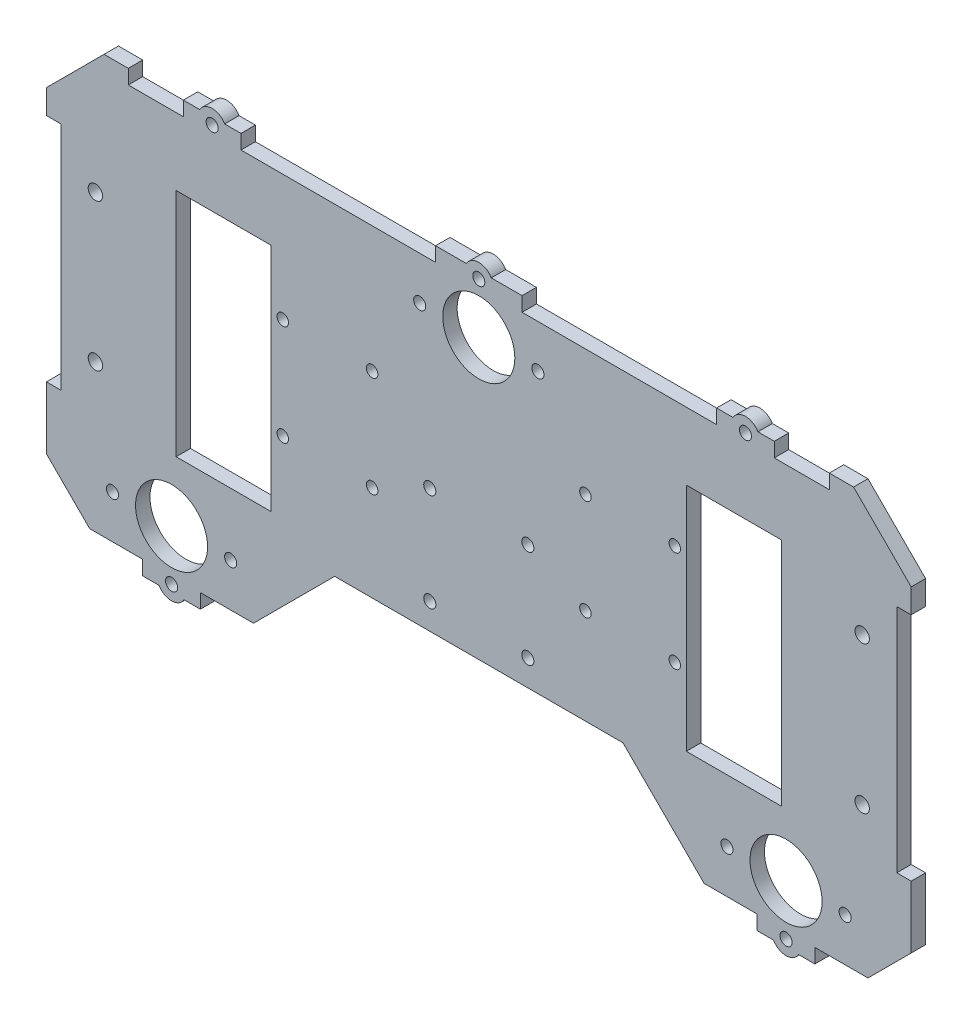
SolidWorks part; units mm, degrees
ref_plane "Front Plane" through (0, 0, 0) normal (0, 0, 1) x (1, 0, 0)
ref_plane "Top Plane" through (0, 0, 0) normal (0, 1, 0) x (1, 0, 0)
ref_plane "Right Plane" through (0, 0, 0) normal (1, 0, 0) x (0, 0, -1)
sketch "Sketch1" plane through (0, 0, 0) normal (0, 0, 1) x (1, 0, 0)
  line L0 (72.8354, 47.1578) -> (72.8354, -32.8422)
  line L1 (105.8354, 47.1578) -> (72.8354, 47.1578)
  line L2 (105.8354, -32.8422) -> (105.8354, 47.1578)
  line L3 (72.8354, -32.8422) -> (105.8354, -32.8422)
  line L4 (84.0016, -74.4431) -> (130.8354, -74.4431)
  line L5 (130.8354, -74.4431) -> (150.8354, -54.4431)
  line L6 (150.8354, -54.4431) -> (150.8354, 55.5569)
  line L7 (150.8354, 55.5569) -> (130.8354, 75.5569)
  line L8 (130.8354, 75.5569) -> (-129.1646, 75.5569)
  line L9 (-129.1646, 75.5569) -> (-149.1646, 55.5569)
  line L10 (-149.1646, 55.5569) -> (-149.1646, -54.4431)
  line L11 (-149.1646, -54.4431) -> (-129.1646, -74.4431)
  line L12 (-129.1646, -74.4431) -> (-82.3309, -74.4431)
  line L13 (-82.3309, -74.4431) -> (-49.1646, -41.2768)
  line L14 (-49.1646, -41.2768) -> (50.8354, -41.2768)
  line L15 (50.8354, -41.2768) -> (84.0016, -74.4431)
  line L16 (-71.1646, -32.8422) -> (-71.1646, 47.1578)
  line L17 (-104.1646, -32.8422) -> (-71.1646, -32.8422)
  line L18 (-104.1646, 47.1578) -> (-104.1646, -32.8422)
  line L19 (-71.1646, 47.1578) -> (-104.1646, 47.1578)
  circle A0 centre (107.4185, -54.4431) radius 12.5
  circle A1 centre (-105.7478, -54.4431) radius 12.5
  circle A2 centre (0.8354, 55.5569) radius 12.5
  dimension "D1" = 45
  dimension "D2" = 45
  dimension "D3" = 28.2843
  dimension "D4" = 110
  dimension "D5" = 28.2843
  dimension "D6" = 46.8338
  dimension "D7" = 46.9042
  dimension "D8" = 100
  dimension "D9" = 46.9042
  dimension "D10" = 46.8338
  dimension "D11" = 28.2843
  dimension "D12" = 110
  dimension "D13" = 28.2843
extrude "Boss-Extrude1" add sketch "Sketch1" along normal blind 5
sketch "Sketch2" plane through (0, 0, 5) normal (0, 0, 1) x (1, 0, 0)
  circle A1 centre (17.3354, -3.2768) radius 1.6
  circle A2 centre (17.3354, -3.2768) radius 1.6
  circle A3 centre (17.3354, -37.2768) radius 1.6
  circle A4 centre (17.3354, -37.2768) radius 1.6
  circle A5 centre (-16.6646, -37.2768) radius 1.6
  circle A6 centre (-16.6646, -37.2768) radius 1.6
  circle A7 centre (-16.6646, -3.2768) radius 1.6
  circle A8 centre (-16.6646, -3.2768) radius 1.6
  dimension "D1" = 0
  dimension "D2" = 0
  dimension "D3" = 0
  dimension "D4" = 0
extrude "Cut-Extrude1" cut sketch "Sketch2" against normal through all
sketch "Sketch4" plane through (0, 0, 5) normal (0, 0, 1) x (1, 0, 0)
  line L0 (150.8354, -54.4431) -> (150.8354, 55.5569) construction
  line L1 (150.8354, 47.1578) -> (145.8354, 47.1578)
  line L2 (150.8354, 47.1578) -> (150.8354, -32.8422)
  line L3 (150.8354, -32.8422) -> (145.8354, -32.8422)
  line L4 (145.8354, 47.1578) -> (145.8354, -32.8422)
  line L5 (105.8354, 47.1578) -> (72.8354, 47.1578) construction
  line L6 (72.8354, -32.8422) -> (105.8354, -32.8422) construction
  line L7 (0.8354, 75.5569) -> (0.8354, 63.8174) construction
  line L8 (130.8354, 75.5569) -> (-129.1646, 75.5569) construction
  line L9 (-144.1646, 47.1578) -> (-144.1646, -32.8422)
  line L10 (-149.1646, -32.8422) -> (-144.1646, -32.8422)
  line L11 (-149.1646, 47.1578) -> (-149.1646, -32.8422)
  line L12 (-149.1646, 47.1578) -> (-144.1646, 47.1578)
  dimension "D1" = 5
extrude "Cut-Extrude3" cut sketch "Sketch4" against normal through all
sketch "Sketch5" plane through (0, 0, 5) normal (0, 0, 1) x (1, 0, 0)
  line L0 (0.8354, 75.5569) -> (0.8354, 46.4183) construction
  line L1 (130.8354, 75.5569) -> (-129.1646, 75.5569) construction
  circle A0 centre (-67.1646, -8.1175) radius 2 construction
  circle A1 centre (-36.1646, -8.1175) radius 2 construction
  circle A2 centre (-36.1646, 26.8825) radius 2 construction
  circle A3 centre (-67.1646, 26.8825) radius 2 construction
  circle A4 centre (-67.1646, -8.1175) radius 2
  circle A5 centre (-36.1646, -8.1175) radius 2
  circle A6 centre (-36.1646, 26.8825) radius 2
  circle A7 centre (-67.1646, 26.8825) radius 2
  circle A8 centre (68.8354, 26.8825) radius 2
  circle A9 centre (37.8354, 26.8825) radius 2
  circle A10 centre (37.8354, -8.1175) radius 2
  circle A11 centre (68.8354, -8.1175) radius 2
extrude "Cut-Extrude4" cut sketch "Sketch5" against normal through all
sketch "Sketch6" plane through (0, 0, 5) normal (0, 0, 1) x (1, 0, 0)
  line L0 (0.8354, 75.5569) -> (0.8354, 62.2242) construction
  line L1 (130.8354, 75.5569) -> (-129.1646, 75.5569) construction
  circle A0 centre (133.8354, -18.3422) radius 2.5 construction
  circle A1 centre (133.8354, 32.6578) radius 2.5 construction
  circle A2 centre (133.8354, -18.3422) radius 2.5
  circle A3 centre (133.8354, 32.6578) radius 2.5
  circle A4 centre (-132.1646, 32.6578) radius 2.5
  circle A5 centre (-132.1646, -18.3422) radius 2.5
extrude "Cut-Extrude5" cut sketch "Sketch6" against normal through all
sketch "Sketch7" plane through (0, 0, 5) normal (0, 0, 1) x (1, 0, 0)
  line L0 (-105.7478, -74.4431) -> (-105.7478, -66.9431) construction
  line L1 (-129.1646, -74.4431) -> (-82.3309, -74.4431) construction
  line L2 (-115.7478, -69.4431) -> (-134.1646, -69.4431)
  line L8 (-115.7478, -74.4431) -> (-115.7478, -69.4431)
  line L10 (-95.7478, -74.4431) -> (-95.7478, -69.4431)
  line L11 (0.8354, -41.2768) -> (0.8354, -58.5234) construction
  line L12 (-49.1646, -41.2768) -> (50.8354, -41.2768) construction
  line L13 (-149.1646, -54.4431) -> (-129.1646, -74.4431) construction
  line L14 (-95.7478, -69.4431) -> (-77.3309, -69.4431)
  line L15 (-82.3309, -74.4431) -> (-49.1646, -41.2768) construction
  line L16 (-134.1646, -69.4431) -> (-129.1646, -74.4431)
  line L17 (-129.1646, -74.4431) -> (-115.7478, -74.4431)
  line L18 (-82.3309, -74.4431) -> (-77.3309, -69.4431)
  line L19 (-95.7478, -74.4431) -> (-82.3309, -74.4431)
  line L20 (107.4185, -74.4431) -> (107.4185, -66.9431) construction
  line L21 (97.4185, -74.4431) -> (84.0016, -74.4431)
  line L22 (84.0016, -74.4431) -> (79.0016, -69.4431)
  line L23 (130.8354, -74.4431) -> (117.4185, -74.4431)
  line L24 (135.8354, -69.4431) -> (130.8354, -74.4431)
  line L25 (97.4185, -69.4431) -> (79.0016, -69.4431)
  line L26 (97.4185, -74.4431) -> (97.4185, -69.4431)
  line L27 (117.4185, -74.4431) -> (117.4185, -69.4431)
  line L28 (117.4185, -69.4431) -> (135.8354, -69.4431)
  circle A0 centre (-105.7478, -54.4431) radius 12.5 construction
  dimension "D1" = 5
  dimension "D2" = 5
  dimension "D3" = 20
  dimension "D4" = 10
extrude "Cut-Extrude7" cut sketch "Sketch7" against normal through all
sketch "Sketch10" plane through (0, 0, 5) normal (0, 0, 1) x (1, 0, 0)
  line L0 (0.8354, 68.0569) -> (0.8354, 75.5569) construction
  line L1 (130.8354, 75.5569) -> (-129.1646, 75.5569) construction
  line L2 (-62.5646, 75.5569) -> (-81.6646, 75.5569) construction
  line L4 (-14.1646, 75.5569) -> (-14.1646, 70.5569)
  line L6 (15.8354, 75.5569) -> (15.8354, 70.5569)
  line L7 (15.8354, 75.5569) -> (64.2354, 75.5569)
  line L8 (15.8354, 75.5569) -> (15.8354, 70.5569)
  line L9 (15.8354, 70.5569) -> (64.2354, 70.5569)
  line L11 (-14.1646, 75.5569) -> (-62.5646, 75.5569)
  line L12 (-14.1646, 75.5569) -> (-14.1646, 70.5569)
  line L13 (-14.1646, 70.5569) -> (-62.5646, 70.5569)
  line L14 (-62.5646, 75.5569) -> (-62.5646, 70.5569)
  line L15 (-91.6646, 75.5569) -> (-91.6646, 70.5569) construction
  line L16 (-101.6646, 75.5569) -> (-120.7646, 75.5569) construction
  line L18 (-101.6646, 75.5569) -> (-101.6646, 70.5569)
  line L20 (-81.6646, 75.5569) -> (-81.6646, 70.5569)
  line L21 (-81.6646, 75.5569) -> (-62.5646, 75.5569)
  line L22 (-81.6646, 75.5569) -> (-81.6646, 70.5569)
  line L23 (-81.6646, 70.5569) -> (-62.5646, 70.5569)
  line L24 (-62.5646, 75.5569) -> (-62.5646, 70.5569)
  line L25 (-101.6646, 75.5569) -> (-120.7646, 75.5569)
  line L26 (-101.6646, 75.5569) -> (-101.6646, 70.5569)
  line L27 (-101.6646, 70.5569) -> (-120.7646, 70.5569)
  line L29 (-120.7646, 75.5569) -> (-120.7646, 70.5569)
  line L30 (15.8354, 75.5569) -> (15.8354, 70.5569)
  line L31 (15.8354, 70.5569) -> (64.2354, 70.5569)
  line L32 (15.8354, 75.5569) -> (64.2354, 75.5569)
  line L33 (83.3354, 75.5569) -> (64.2354, 75.5569)
  line L34 (83.3354, 70.5569) -> (64.2354, 70.5569)
  line L35 (83.3354, 75.5569) -> (83.3354, 70.5569)
  line L36 (103.3354, 75.5569) -> (103.3354, 70.5569)
  line L37 (103.3354, 75.5569) -> (122.4354, 75.5569)
  line L38 (122.4354, 75.5569) -> (122.4354, 70.5569)
  line L39 (103.3354, 70.5569) -> (122.4354, 70.5569)
  line L40 (-149.1646, 55.5569) -> (-149.1646, 47.1578) construction
  line L41 (-149.1646, 55.5569) -> (-149.1646, 47.1578)
  circle A0 centre (0.8354, 55.5569) radius 12.5 construction
  dimension "D1" = 5
  dimension "D2" = 19.1
  dimension "D3" = 15
  dimension "D4" = 19.1
  dimension "D5" = 48.4
  dimension "D10" = 8.4
  dimension "D11" = 5
extrude "Cut-Extrude9" cut sketch "Sketch10" against normal through all contours L25 L29 L27 L18 | L20 L23 L14 L21 | L11 L14 L13 L4 | L35 L33 L7 L6 L9 L34 | L36 L39 L38 L37
sketch "Sketch11" plane through (0, 0, 5) normal (0, 0, 1) x (1, 0, 0)
  line L0 (-14.1646, 75.5569) -> (15.8354, 70.5569) construction
  line L1 (-101.6646, 75.5569) -> (-81.6646, 70.5569) construction
  line L2 (83.3354, 75.5569) -> (103.3354, 70.5569) construction
  line L3 (-115.7478, -74.4431) -> (-95.7478, -69.4431) construction
  line L4 (97.4185, -74.4431) -> (117.4185, -69.4431) construction
  line L5 (97.4185, -74.4431) -> (117.4185, -74.4431) construction
  line L6 (-115.7478, -74.4431) -> (-95.7478, -74.4431) construction
  line L7 (103.3354, 75.5569) -> (83.3354, 75.5569) construction
  line L8 (15.8354, 75.5569) -> (-14.1646, 75.5569) construction
  line L9 (-81.6646, 75.5569) -> (-101.6646, 75.5569) construction
  line L10 (103.0884, -74.4431) -> (111.7486, -74.4431)
  line L11 (-110.0779, -74.4431) -> (-101.4176, -74.4431)
  line L12 (97.6655, 75.5569) -> (89.0052, 75.5569)
  line L13 (5.1655, 75.5569) -> (-3.4948, 75.5569)
  line L14 (-87.3345, 75.5569) -> (-95.9948, 75.5569)
  arc A0 (-87.3345, 75.5569) -> (-95.9948, 75.5569) centre (-91.6646, 73.0569) ccw
  arc A1 (5.1655, 75.5569) -> (-3.4948, 75.5569) centre (0.8354, 73.0569) ccw
  arc A2 (97.6655, 75.5569) -> (89.0052, 75.5569) centre (93.3354, 73.0569) ccw
  arc A3 (-110.0779, -74.4431) -> (-101.4176, -74.4431) centre (-105.7478, -71.9431) ccw
  arc A4 (103.0884, -74.4431) -> (111.7486, -74.4431) centre (107.4185, -71.9431) ccw
  dimension "D1" = 10
  dimension "D2" = 10
  dimension "D3" = 10
  dimension "D4" = 10
  dimension "D5" = 10
extrude "Boss-Extrude3" add sketch "Sketch11" against normal blind 5
sketch "Sketch12" plane through (0, 0, 5) normal (0, 0, 1) x (1, 0, 0)
  line L0 (-14.1646, 75.5569) -> (15.8354, 70.5569) construction
  line L1 (-101.6646, 75.5569) -> (-81.6646, 70.5569) construction
  line L2 (83.3354, 75.5569) -> (103.3354, 70.5569) construction
  line L3 (-115.7478, -69.4431) -> (-95.7478, -74.4431) construction
  line L4 (97.4185, -74.4431) -> (117.4185, -69.4431) construction
  circle A0 centre (107.4185, -71.9431) radius 2.1
  circle A1 centre (-105.7478, -71.9431) radius 2.1
  circle A2 centre (93.3354, 73.0569) radius 2.1
  circle A3 centre (0.8354, 73.0569) radius 2.1
  circle A4 centre (-91.6646, 73.0569) radius 2.1
  dimension "D1" = 4.2
  dimension "D2" = 4.2
  dimension "D3" = 4.2
  dimension "D4" = 4.2
  dimension "D5" = 4.2
extrude "Cut-Extrude10" cut sketch "Sketch12" against normal blind 5
sketch "Sketch13" plane through (0, 0, 5) normal (0, 0, 1) x (1, 0, 0)
  line L0 (-24.269, 55.5569) -> (23.8406, 55.5569) construction
  line L1 (0.8354, -41.2768) -> (0.8354, -57.9375) construction
  line L2 (-49.1646, -41.2768) -> (50.8354, -41.2768) construction
  line L3 (-130.5718, -54.4431) -> (-80.3209, -54.4431) construction
  line L4 (132.2425, -54.4431) -> (81.9916, -54.4431) construction
  circle A0 centre (-19.6646, 55.5569) radius 2.1
  circle A1 centre (21.3354, 55.5569) radius 2.1
  circle A2 centre (-126.2478, -54.4431) radius 2.1
  circle A3 centre (-85.2478, -54.4431) radius 2.1
  circle A5 centre (-105.7478, -54.4431) radius 12.5 construction
  circle A6 centre (0.8354, 55.5569) radius 12.5 construction
  circle A7 centre (86.9185, -54.4431) radius 2.1
  circle A8 centre (127.9185, -54.4431) radius 2.1
  dimension "D1" = 4.2
  dimension "D2" = 20.5
  dimension "D3" = 4.2
  dimension "D4" = 20.5
  dimension "D5" = 4.2
  dimension "D6" = 4.2
  dimension "D7" = 20.5
  dimension "D8" = 20.5
extrude "Cut-Extrude11" cut sketch "Sketch13" against normal blind 5
sketch "Sketch15" plane through (0, 0, 0) normal (0, 0, -1) x (-1, 0, 0)
  circle A1 centre (16.6646, -37.2768) radius 1.6
  circle A2 centre (16.6646, -37.2768) radius 1.6
  circle A3 centre (16.6646, -3.2768) radius 1.6
  circle A4 centre (16.6646, -3.2768) radius 1.6
  circle A5 centre (-17.3354, -37.2768) radius 1.6
  circle A6 centre (-17.3354, -37.2768) radius 1.6
  circle A7 centre (-17.3354, -3.2768) radius 1.6
  circle A8 centre (-17.3354, -3.2768) radius 1.6
  dimension "D1" = 0
  dimension "D2" = 0
  dimension "D3" = 0
  dimension "D4" = 0
extrude "Boss-Extrude4" add sketch "Sketch15" against normal up to surface (5 mm away) up to face at (125.8185, -54.4431, 5)
sketch "Sketch17" plane through (0, 0, 5) normal (0, 0, 1) x (1, 0, 0)
  line L0 (0.8354, 10.7232) -> (0.8354, -21.7842) construction
  line L1 (26.8354, -15.2768) -> (-19.8624, -15.2768) construction
  circle A0 centre (-16.1646, 1.7232) radius 2.1
  circle A1 centre (17.8354, 1.7232) radius 2.1
  circle A2 centre (17.8354, -32.2768) radius 2.1
  circle A3 centre (-16.1646, -32.2768) radius 2.1
  dimension "D1" = 4.2
extrude "Cut-Extrude13" cut sketch "Sketch17" against normal through all
